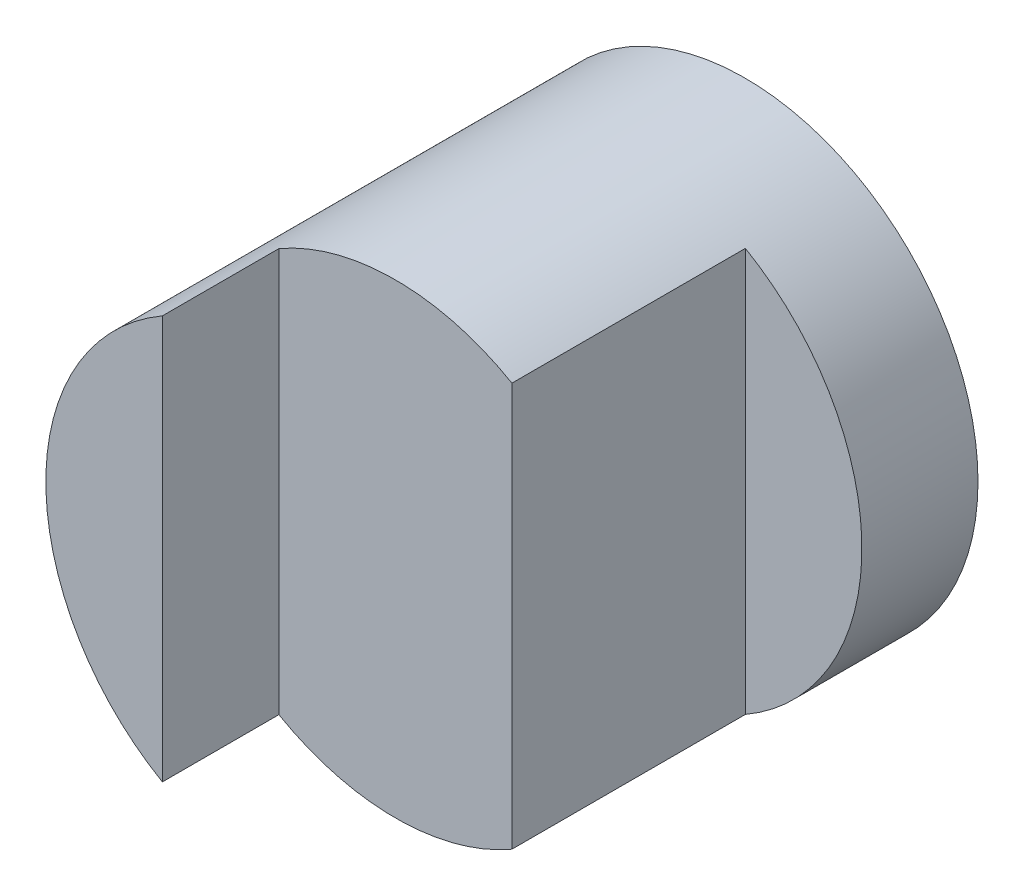
SolidWorks part; units mm, degrees
ref_plane "Front" through (0, 0, 0) normal (0, 0, 1) x (1, 0, 0)
ref_plane "Top" through (0, 0, 0) normal (0, 1, 0) x (1, 0, 0)
ref_plane "Right" through (0, 0, 0) normal (1, 0, 0) x (0, 0, -1)
sketch "Sketch1" plane through (0, 0, 0) normal (0, 0, 1) x (1, 0, 0)
  circle A0 centre (0, 0) radius 2
  dimension "D1" = 4
extrude "Boss-Extrude1" add sketch "Sketch1" along normal blind 4
sketch "Sketch2" plane through (0, 0, 0) normal (0, 1, 0) x (1, 0, 0)
  line L0 (-2, -4) -> (2, -4) construction
  line L3 (-1, -3) -> (1, -3)
  line L5 (0, -4) -> (1, -3) construction
  line L6 (-1, -3) -> (0, -4) construction
  line L12 (-1, -3) -> (-1, -4)
  line L13 (-1, -4) -> (2, -4)
  line L14 (2, -4) -> (2, -0.9964)
  line L15 (2, -4) -> (2, 0) construction
  line L16 (2, -0.9964) -> (1, -0.9964)
  line L17 (1, -0.9964) -> (1, -3)
  point P0 (0, -4)
  dimension "D1" = 2
extrude "Cut-Extrude2" cut sketch "Sketch2" against normal mid plane 4
